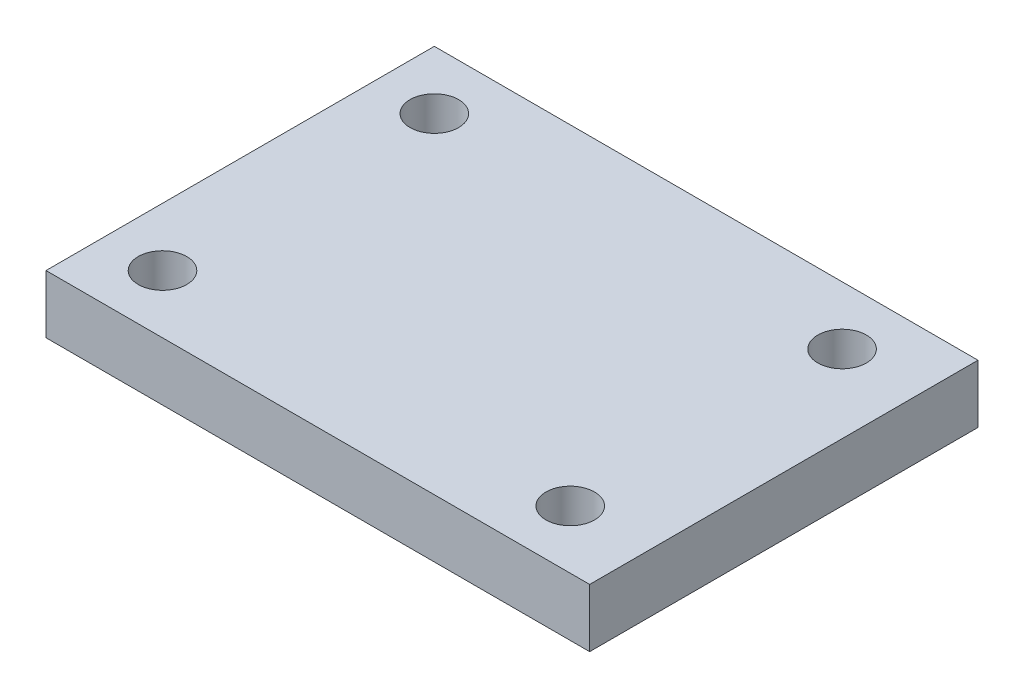
SolidWorks part; units mm, degrees
ref_plane "Front Plane" through (0, 0, 0) normal (0, 0, 1) x (1, 0, 0)
ref_plane "Top Plane" through (0, 0, 0) normal (0, 1, 0) x (1, 0, 0)
ref_plane "Right Plane" through (0, 0, 0) normal (1, 0, 0) x (0, 0, -1)
sketch "Эскиз1" plane through (0, 0, 0) normal (0, 1, 0) x (1, 0, 0)
  line L0 (0, 0) -> (28, 0)
  line L1 (0, 0) -> (0, 20)
  line L2 (28, 0) -> (28, 20)
  line L3 (0, 20) -> (28, 20)
  line L4 (0, 10) -> (28, 10) construction
  line L5 (14, 20) -> (14, 0) construction
  point P6 (3, 17)
  point P8 (3, 3)
  point P12 (25, 3)
  point P13 (25, 17)
  dimension "D1" = 28
  dimension "D2" = 20
  dimension "D3" = 3
  dimension "D4" = 14
extrude "Бобышка-Вытянуть1" add sketch "Эскиз1" along normal blind 3
sketch "Эскиз2" plane through (0, 3, 0) normal (0, 1, 0) x (1, 0, 0)
  line L0 (0, 20) -> (0, 0) construction
  line L1 (0, 10) -> (14, 10) construction
  point P0 (3, 17)
  point P5 (24, 17)
  point P7 (24, 3)
  point P11 (3, 3)
  dimension "D1" = 3
  dimension "D2" = 14
  dimension "D3" = 21
hole_wizard "Отверстие обработанное метчиком M31" positions "Эскиз3" profile "Эскиз4" tap size "M3" standard "DIN" end condition through all
sketch "Эскиз3" plane through (0, 3, 0) normal (0, 1, 0) x (1, 0, 0)
  point P0 (3, 17)
  point P3 (3, 3)
  point P6 (24, 3)
  point P9 (24, 17)
sketch "Эскиз4" plane through (3, 3, -17) normal (1, 0, 0) x (0, 0, 1)
  line L0 (0, 0) -> (0, 3)
  line L1 (0, 3) -> (1.25, 3)
  line L2 (1.25, 3) -> (1.25, 0)
  line L5 (1.25, 0) -> (0, 0)
  line L11 (0, -6.35) -> (0, 107.95) construction
  dimension "Диаметр проходного сверла" = 2.5
  dimension "Глубина проходного сверла" = 3
cosmetic thread "Отверстие резьбы5" parameters "D2"=3
cosmetic thread "Отверстие резьбы6" parameters "D2"=3
cosmetic thread "Отверстие резьбы7" parameters "D2"=3
cosmetic thread "Отверстие резьбы8" parameters "D2"=3
